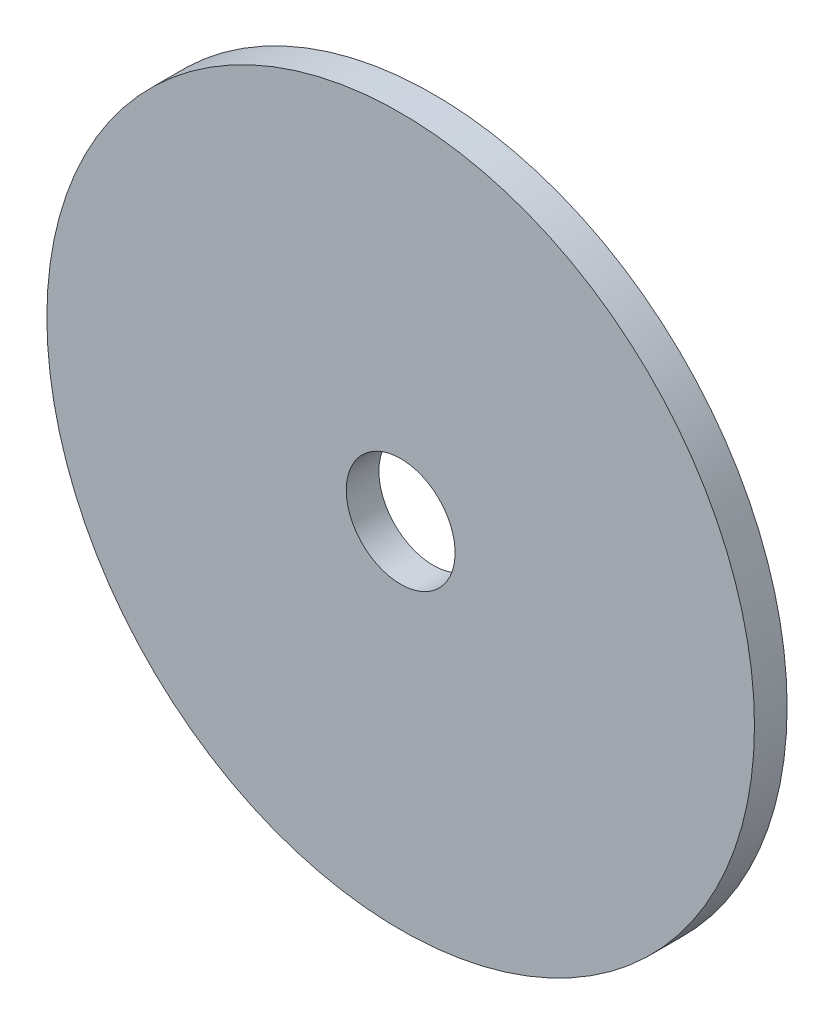
SolidWorks part; units mm, degrees
ref_plane "Front Plane" through (0, 0, 0) normal (0, 0, 1) x (1, 0, 0)
ref_plane "Top Plane" through (0, 0, 0) normal (0, 1, 0) x (1, 0, 0)
ref_plane "Right Plane" through (0, 0, 0) normal (1, 0, 0) x (0, 0, -1)
sketch "Sketch1" plane through (0, 0, 0) normal (0, 0, 1) x (1, 0, 0)
  circle A0 centre (0, 0) radius 65
  dimension "D1" = 130
extrude "Boss-Extrude1" add sketch "Sketch1" along normal blind 6
sketch "Sketch4" plane through (0, 0, 0) normal (0, 0, -1) x (-1, 0, 0)
  circle A0 centre (0, 0) radius 10
  dimension "D1" = 20
extrude "Cut-Extrude3" cut sketch "Sketch4" against normal through all
